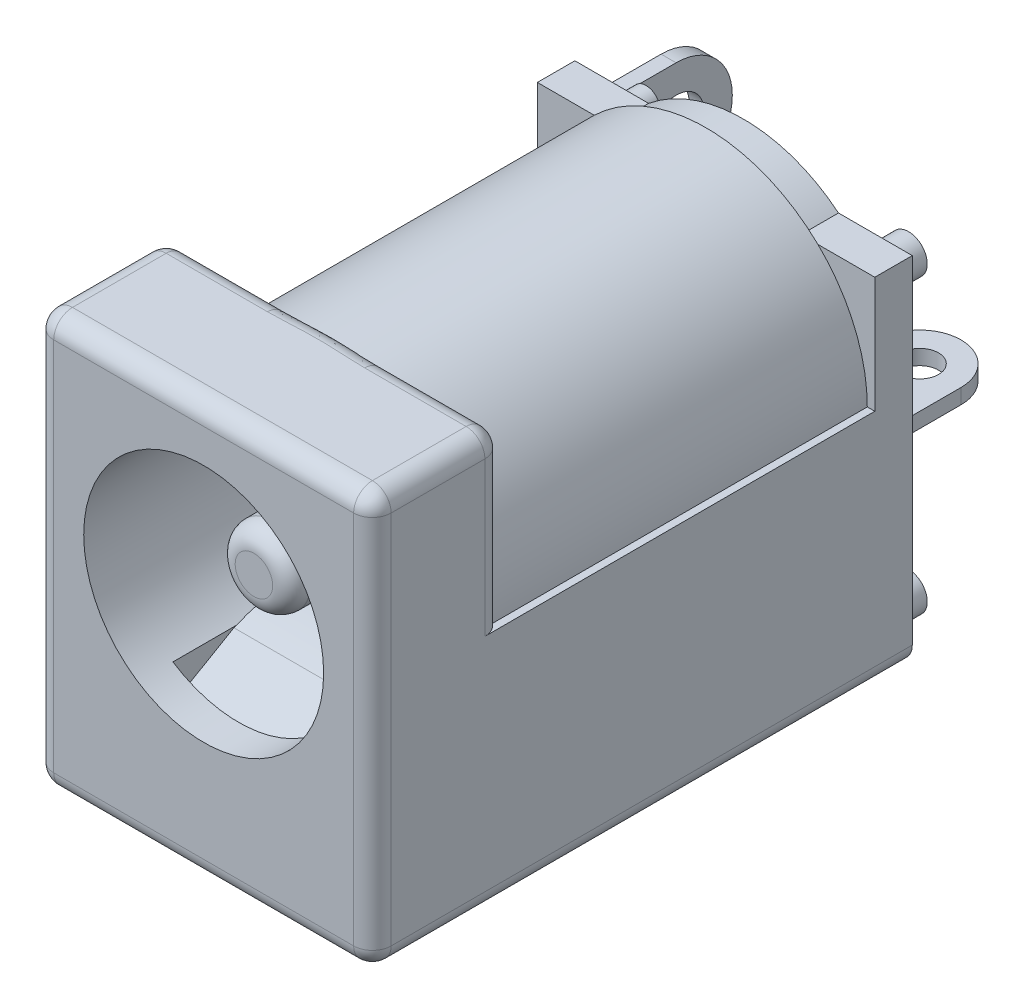
SolidWorks part; units mm, degrees
material "ABS"
ref_plane "Plane1" through (0, 0, 0) normal (0, 0, 1) x (1, 0, 0)
ref_plane "Plane2" through (0, 0, 0) normal (0, 1, 0) x (1, 0, 0)
ref_plane "Plane3" through (0, 0, 0) normal (1, 0, 0) x (0, 0, -1)
sketch "Sketch1" plane through (0, 0, 0) normal (0, 0, 1) x (1, 0, 0)
  line L0 (-4.5, 5.5) -> (4.5, 5.5) construction
  line L1 (-4.5, 0) -> (4.5, 0)
  line L2 (-4.5, 0) -> (-4.5, 11)
  line L3 (-4.5, 11) -> (4.5, 11)
  line L4 (4.5, 0) -> (4.5, 11)
  line L5 (0, 11) -> (0, 0) construction
  dimension "D1" = 9
  dimension "D2" = 11
extrude "Base-Extrude" add sketch "Sketch1" against normal blind 3.5
sketch "Sketch2" plane through (0, 0, -3.5) normal (0, 0, -1) x (-1, 0, 0)
  line L0 (4.5, 0) -> (-4.5, 0) construction
  line L1 (-4.5, 0) -> (-4.5, 11) construction
  line L2 (4.5, 11) -> (4.5, 0) construction
  line L3 (-4.5, 0) -> (-4.5, 6.4)
  line L4 (4.5, 0) -> (-4.5, 0)
  line L5 (4.5, 6.4) -> (4.5, 0)
  line L6 (-4.3, 6.4) -> (-4.5, 6.4)
  line L7 (4.3, 6.4) -> (4.5, 6.4)
  arc A0 (-4.3, 6.4) -> (4.3, 6.4) centre (0, 6.4) cw
  dimension "D1" = 4.3
  dimension "D2" = 6.4
extrude "Boss-Extrude1" add sketch "Sketch2" along normal blind 9.9
sketch "Sketch3" plane through (0, 0, 0) normal (0, 0, 1) x (1, 0, 0)
  circle A0 centre (0, 6.4) radius 3.2
  dimension "D1" = 6.4
  dimension "D2" = 6.4
extrude "Cut-Extrude1" cut sketch "Sketch3" against normal blind 9.144
sketch "Sketch4" plane through (0, 0, -9.144) normal (0, 0, 1) x (1, 0, 0)
  circle A0 centre (0, 6.4) radius 1
  dimension "D1" = 2
extrude "Extrude1" add sketch "Sketch4" along normal offset from surface (7.804 mm away) 1.34 up to face at (3.2, 6.4, 0)
fillet "Fillet1" radius 0.5 1 edges at (-1, 6.4, -1.34)
sketch "Sketch21" plane through (0, 0, -13.4) normal (0, 0, -1) x (-1, 0, 0)
  line L0 (2.532, 9.4966) -> (4.5, 9.4966)
  line L1 (-4.5, 9.4966) -> (-2.532, 9.4966)
  line L2 (-4.5, 9.4966) -> (-4.5, 6.4)
  line L4 (4.5, 9.4966) -> (4.5, 6.4)
  line L5 (-4.3, 6.4) -> (-4.5, 6.4)
  line L6 (-4.5, 6.4) -> (-4.5, 0)
  line L7 (-4.5, 0) -> (4.5, 0)
  line L8 (4.5, 0) -> (4.5, 6.4)
  line L9 (4.5, 6.4) -> (4.3, 6.4)
  line L11 (-4.5, 6.4) -> (-4.5, 0)
  line L12 (-4.5, 0) -> (4.5, 0)
  line L13 (4.5, 0) -> (4.5, 6.4)
  arc A0 (2.532, 9.4966) -> (-2.532, 9.4966) centre (0, 6.4) ccw
  arc A1 (4.3, 6.4) -> (-4.3, 6.4) centre (0, 6.4) ccw
  point P12 (2.7753, 9.2806)
  point P13 (-2.7753, 9.2806)
  dimension "D1" = 0
extrude "Boss-Extrude2" add sketch "Sketch21" along normal blind 1
ref_plane "Plane4" through (-4.9, 0, 0) normal (1, 0, 0) x (0, 0, -1)
sketch "Sketch22" plane through (0, 0, -14.4) normal (0, 0, -1) x (-1, 0, 0)
  line L1 (2.555, 7.9) -> (4.9, 7.9)
  line L2 (0, 6.4) -> (2.9166, 6.4) construction
  line L3 (2.555, 4.9) -> (4.9, 4.9)
  line L4 (4.9, 7.9) -> (4.9, 4.9)
  line L5 (2.555, 7.9) -> (2.555, 8.434)
  line L6 (2.555, 4.366) -> (0, 4.366)
  line L7 (2.555, 4.366) -> (2.555, 4.9)
  line L8 (2.555, 8.434) -> (0, 8.434)
  line L10 (2.3158, 6.7076) -> (2.729, 6.7076)
  line L11 (2.3158, 6.7076) -> (2.3158, 6.1265)
  line L12 (2.3158, 6.1265) -> (2.729, 6.1265)
  line L13 (2.729, 6.7076) -> (2.729, 6.1265)
  arc A0 (0, 8.434) -> (0, 4.366) centre (0, 6.4) ccw
  dimension "D1" = 3
  dimension "D2" = 4.9
extrude "Boss-Extrude3" add sketch "Sketch22" along normal blind 0.4
sketch "Sketch23" plane through (0, 0, -14.4) normal (0, 0, -1) x (-1, 0, 0)
  line L0 (0, 0) -> (0, 3.7044) construction
  line L1 (-3.5, 8.6) -> (3.5, 8.6) construction
  line L2 (-3.5, 8.6) -> (-3.5, 0.8) construction
  line L3 (-3.5, 0.8) -> (3.5, 0.8) construction
  line L4 (3.5, 8.6) -> (3.5, 0.8) construction
  line L5 (-4.5, 0) -> (4.5, 0) construction
  circle A0 centre (-3.5, 0.8) radius 0.5
  circle A1 centre (3.5, 0.8) radius 0.5
  circle A2 centre (-3.5, 8.6) radius 0.5
  circle A3 centre (3.5, 8.6) radius 0.375
  arc A4 (0, 8.434) -> (0, 4.366) centre (0, 6.4) ccw construction
  dimension "D3" = 5.6
  dimension "D4" = 1
  dimension "D5" = 0.75
  dimension "D1" = 7
  dimension "D2" = 7.8
extrude "Boss-Extrude4" add sketch "Sketch23" along normal blind 0.9
sketch "Sketch24" plane through (0, 0, -14.4) normal (0, 0, -1) x (-1, 0, 0)
  line L0 (-2.5, 3.6) -> (-0.3, 3.6) construction
  line L1 (-2.5, 3.8) -> (-0.3, 3.8)
  line L2 (-2.5, 3.8) -> (-2.5, 3.4)
  line L3 (-2.5, 3.4) -> (-0.3, 3.4)
  line L4 (-0.3, 3.8) -> (-0.3, 3.4)
  line L5 (0.3, 0.925) -> (2.5, 0.925)
  line L6 (0.3, 0.925) -> (0.3, 0.675)
  line L7 (0.3, 0.675) -> (2.5, 0.675)
  line L8 (2.5, 0.925) -> (2.5, 0.675)
  line L9 (0.3, 0.8) -> (2.5, 0.8) construction
  line L10 (1.4, 0.925) -> (1.4, 0.675) construction
  line L11 (-1.4, 3.8) -> (-1.4, 3.4) construction
  line L12 (0, 0) -> (0, 1.7579) construction
  line L13 (-4.5, 0) -> (4.5, 0) construction
  arc A0 (0, 8.434) -> (0, 4.366) centre (0, 6.4) ccw construction
  dimension "D1" = 0.4
  dimension "D2" = 0.25
  dimension "D3" = 2.2
  dimension "D4" = 2.2
  dimension "D5" = 2.8
  dimension "D6" = 2.8
  dimension "D7" = 2.8
extrude "Boss-Extrude5" add sketch "Sketch24" along normal blind 4.4
sketch "Sketch5" plane through (-4.9, 0, 0) normal (1, 0, 0) x (0, 0, -1)
  line L0 (14.4, 7.9) -> (17.3, 7.9)
  line L1 (14.4, 4.9) -> (17.3, 4.9)
  line L2 (14.4, 4.9) -> (14.4, 7.9)
  line L3 (14.4, 4.9) -> (14.4, 7.9) construction
  line L4 (14.4, 4.9) -> (14.4, 7.9) construction
  arc A0 (17.3, 7.9) -> (17.3, 4.9) centre (17.3, 6.4) cw
  circle A1 centre (17.3, 6.4) radius 0.75
  dimension "D5" = 1.5
  dimension "D1" = 2.9
extrude "Extrude2" add sketch "Sketch5" along normal mid plane 0.4
sketch "Sketch25" plane through (0, 3.8, 0) normal (0, 1, 0) x (1, 0, 0)
  line L0 (0.3, 17.7) -> (0.3, 18.8)
  line L1 (0.3, 18.8) -> (1.8148, 19.1278)
  line L2 (1.8148, 19.1278) -> (2.5, 18.8)
  line L3 (0.3, 18.8) -> (2.5, 18.8) construction
  line L4 (2.5, 18.8) -> (2.5, 17.7)
  line L5 (-2.5, 17.7) -> (-2.5, 18.8)
  line L6 (-2.5, 18.8) -> (-1.3889, 19.1278)
  line L7 (-1.3889, 19.1278) -> (-0.3, 18.8)
  line L8 (-0.3, 18.8) -> (-0.3, 17.7)
  line L9 (-0.3, 18.8) -> (-0.3, 14.4) construction
  line L10 (-2.5, 18.8) -> (-0.3, 18.8) construction
  line L11 (2.5, 18.8) -> (2.5, 14.4) construction
  arc A0 (2.5, 17.7) -> (0.3, 17.7) centre (1.4, 17.7) ccw
  arc A1 (-0.3, 17.7) -> (-2.5, 17.7) centre (-1.4, 17.7) ccw
  circle A2 centre (-1.4, 17.7) radius 0.5
  circle A3 centre (1.4, 17.7) radius 0.5
  dimension "D1" = 1
  dimension "D2" = 1
extrude "Cut-Extrude5" cut sketch "Sketch25" against normal blind 12.2
sketch "Sketch26" plane through (0, 0, -14.8) normal (0, 0, -1) x (-1, 0, 0)
  circle A0 centre (0.1979, 6.4) radius 1.2353
extrude "Boss-Extrude6" add sketch "Sketch26" along normal blind 0.3
fillet "Fillet2" radius 0.5 11 edges at (0, 11, 0) (4.5, 5.5, 0) (0, 0, 0) (-4.5, 5.5, 0) (4.5, 0, -7.2) (-4.5, 0, -7.2) (4.5, 11, -1.75) (0, 11, -3.5) (-4.5, 11, -1.75)
sketch "Sketch28" plane through (0, 0, 0) normal (1, 0, 0) x (0, 0, -1)
  line L1 (0.9301, 4.9549) -> (9.13, 4.9549)
  line L2 (0.9301, 4.9549) -> (0.9301, 1.0645)
  line L3 (0.9301, 1.0645) -> (9.13, 1.0645)
  line L4 (9.13, 4.9549) -> (9.13, 1.0645)
extrude "Cut-Extrude6" cut sketch "Sketch28" against normal mid plane 3.5
sketch "Sketch27" plane through (0, 0, 0) normal (1, 0, 0) x (0, 0, -1)
  line L0 (0.8551, 3.1051) -> (2.3067, 3.9462)
  line L1 (6.1256, 3.9462) -> (9.0599, 2.6851)
  line L2 (1.0055, 2.8455) -> (2.4414, 3.6775)
  line L3 (6.0071, 3.6705) -> (8.9415, 2.4095)
  line L4 (9.0599, 2.6851) -> (8.9415, 2.4095)
  line L5 (0.8551, 3.1051) -> (1.0055, 2.8455)
  arc A0 (2.3067, 3.9462) -> (6.1256, 3.9462) centre (4.2162, -0.497) cw
  arc A1 (2.4414, 3.6775) -> (6.0071, 3.6705) centre (4.2162, -0.497) cw
  dimension "D1" = 0.3
extrude "Boss-Extrude7" add sketch "Sketch27" along normal mid plane 3
